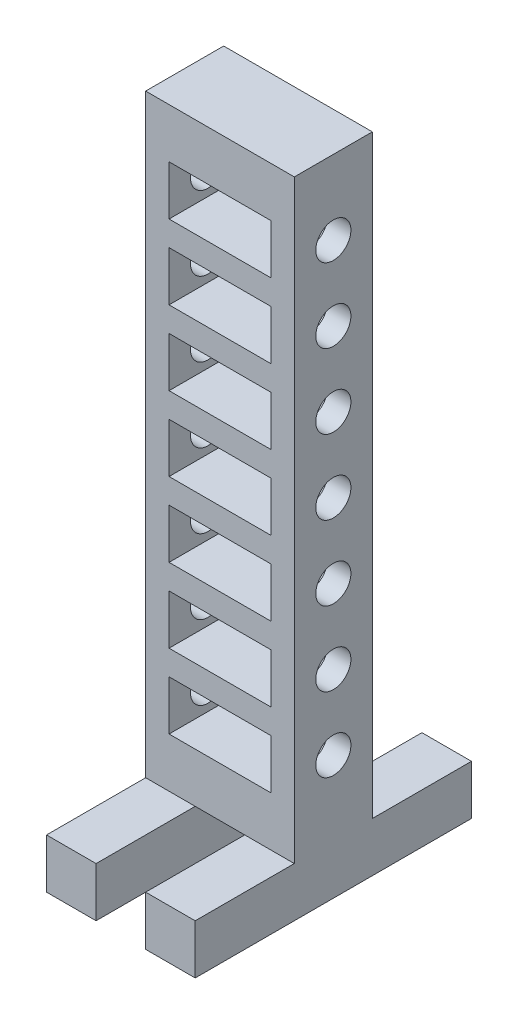
SolidWorks part; units mm, degrees
ref_plane "Front Plane" through (0, 0, 0) normal (0, 0, 1) x (1, 0, 0)
ref_plane "Top Plane" through (0, 0, 0) normal (0, 1, 0) x (1, 0, 0)
ref_plane "Right Plane" through (0, 0, 0) normal (1, 0, 0) x (0, 0, -1)
sketch "Sketch1" plane through (0, 0, 0) normal (0, 0, 1) x (1, 0, 0)
  line L1 (0, 0) -> (19.05, 0)
  line L2 (0, 0) -> (0, 76.2)
  line L3 (0, 76.2) -> (19.05, 76.2)
  line L4 (19.05, 0) -> (19.05, 76.2)
  line L5 (3, 69.85) -> (16.05, 69.85)
  line L6 (3, 69.85) -> (3, 63.5)
  line L7 (3, 63.5) -> (16.05, 63.5)
  line L8 (16.05, 69.85) -> (16.05, 63.5)
  line L9 (3, 60.325) -> (16.05, 60.325)
  line L10 (3, 60.325) -> (3, 53.975)
  line L11 (3, 53.975) -> (16.05, 53.975)
  line L12 (16.05, 60.325) -> (16.05, 53.975)
  line L13 (3, 50.8) -> (16.05, 50.8)
  line L14 (3, 50.8) -> (3, 44.45)
  line L15 (3, 44.45) -> (16.05, 44.45)
  line L16 (16.05, 50.8) -> (16.05, 44.45)
  line L17 (3, 41.275) -> (16.05, 41.275)
  line L18 (3, 41.275) -> (3, 34.925)
  line L19 (3, 34.925) -> (16.05, 34.925)
  line L20 (16.05, 41.275) -> (16.05, 34.925)
  line L21 (3, 31.75) -> (16.05, 31.75)
  line L22 (3, 31.75) -> (3, 25.4)
  line L23 (3, 25.4) -> (16.05, 25.4)
  line L24 (16.05, 31.75) -> (16.05, 25.4)
  line L25 (3, 22.225) -> (16.05, 22.225)
  line L26 (3, 22.225) -> (3, 15.875)
  line L27 (3, 15.875) -> (16.05, 15.875)
  line L28 (16.05, 22.225) -> (16.05, 15.875)
  line L29 (3, 12.7) -> (16.05, 12.7)
  line L30 (3, 12.7) -> (3, 6.35)
  line L31 (3, 6.35) -> (16.05, 6.35)
  line L32 (16.05, 12.7) -> (16.05, 6.35)
  dimension "D1" = 19.05
  dimension "D2" = 76.2
  dimension "D3" = 6.35
  dimension "D4" = 3
  dimension "D5" = 3
  dimension "D6" = 6.35
  dimension "D7" = 3.175
  dimension "D8" = 3.175
  dimension "D9" = 3.175
  dimension "D10" = 3.175
  dimension "D11" = 3.175
  dimension "D12" = 3.175
extrude "Boss-Extrude1" add sketch "Sketch1" along normal blind 10
sketch "Sketch2" plane through (0, 0, 0) normal (0, -1, 0) x (1, 0, 0)
  line L0 (0, 10) -> (0, 0) construction
  line L1 (0, 22.7) -> (6.35, 22.7)
  line L2 (0, 22.7) -> (0, -12.7)
  line L3 (0, -12.7) -> (6.35, -12.7)
  line L4 (6.35, 22.7) -> (6.35, -12.7)
  line L5 (19.05, 22.7) -> (12.7, 22.7)
  line L6 (19.05, 22.7) -> (19.05, -12.7)
  line L7 (19.05, -12.7) -> (12.7, -12.7)
  line L8 (12.7, 22.7) -> (12.7, -12.7)
  line L9 (19.05, 10) -> (19.05, 0) construction
  line L10 (0, 10) -> (19.05, 10) construction
  line L11 (0, 0) -> (19.05, 0) construction
  dimension "D1" = 12.7
  dimension "D2" = 12.7
  dimension "D3" = 6.35
extrude "Boss-Extrude2" add sketch "Sketch2" along normal blind 6.35
sketch "Sketch3" plane through (19.05, 0, 0) normal (1, 0, 0) x (0, 0, -1)
  line L2 (-10, 0) -> (-10, 76.2) construction
  line L3 (-10, 76.2) -> (0, 76.2) construction
  circle A0 centre (-5, 66.675) radius 2.25
  circle A1 centre (-5, 57.15) radius 2.25
  circle A2 centre (-5, 47.625) radius 2.25
  circle A3 centre (-5, 38.1) radius 2.25
  circle A4 centre (-5, 28.575) radius 2.25
  circle A5 centre (-5, 19.05) radius 2.25
  circle A6 centre (-5, 9.525) radius 2.25
  point P16 (0, 0)
  dimension "D1" = 5
  dimension "D3" = 4.5
  dimension "D4" = 9.525
  dimension "D9" = 9.525
  dimension "D2" = 9.525
  dimension "D5" = 9.525
  dimension "D6" = 9.525
  dimension "D7" = 9.525
  dimension "D8" = 9.525
extrude "Cut-Extrude1" cut sketch "Sketch3" against normal blind 30
